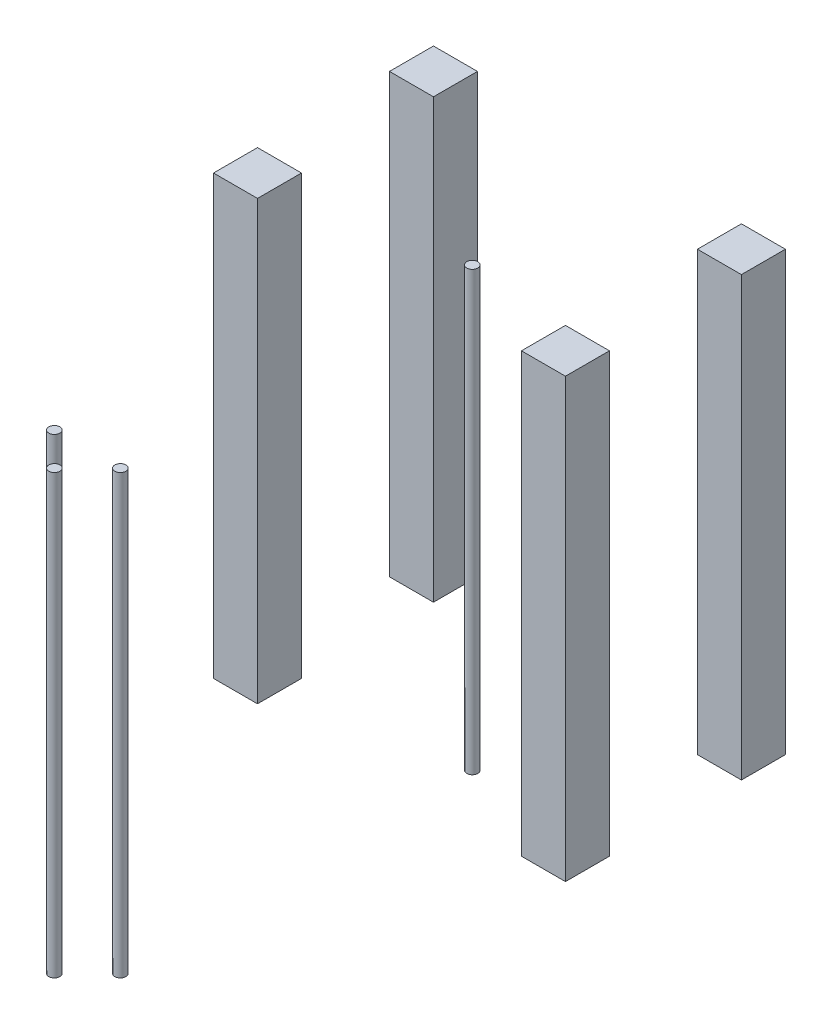
SolidWorks part; units mm, degrees
ref_plane "Ebene vorne" through (0, 0, 0) normal (0, 0, 1) x (1, 0, 0)
ref_plane "Ebene oben" through (0, 0, 0) normal (0, 1, 0) x (1, 0, 0)
ref_plane "Ebene rechts" through (0, 0, 0) normal (1, 0, 0) x (0, 0, -1)
sketch "Top" plane through (0, 0, 0) normal (0, 1, 0) x (1, 0, 0)
  line L0 (0, -95) -> (0, -285) construction
  line L1 (55, -285) -> (55, -95)
  line L2 (55, -285) -> (-55, -285)
  line L3 (-55, -285) -> (-55, -95)
  line L4 (55, -95) -> (-55, -95)
  line L5 (55, -285) -> (-55, -95) construction
  line L6 (-55, -285) -> (55, -95) construction
  line L16 (0, -190) -> (0, -150.9424) construction
  line L27 (-30, -285) -> (-30, -255)
  line L28 (-30, -285) -> (30, -285)
  line L29 (30, -285) -> (30, -255)
  line L30 (-30, -255) -> (30, -255)
  line L31 (0, -255) -> (-30, -255)
  line L32 (30, -255) -> (-30, -255)
  line L34 (30, -285) -> (-30, -285)
  line L35 (0, -190) -> (89.9295, -190) construction
  line L36 (30, -95) -> (-30, -95)
  line L39 (0, -125) -> (-30, -125)
  line L40 (-30, -125) -> (30, -125)
  line L41 (30, -95) -> (30, -125)
  line L42 (-30, -95) -> (30, -95)
  line L43 (-30, -95) -> (-30, -125)
  circle A0 centre (-15, -270) radius 3
  circle A1 centre (15, -270) radius 3
  circle A4 centre (15, -270) radius 3
  circle A5 centre (-15, -270) radius 3
  circle A6 centre (-15, -110) radius 3
  circle A7 centre (15, -110) radius 3
  circle A8 centre (15, -110) radius 3
  circle A9 centre (-15, -110) radius 3
  point P33 (0, -190)
sketch "BaseplateHeight" plane through (0, 0, 0) normal (1, 0, 0) x (0, 0, -1)
  line L1 (-95, 205) -> (-285, 205)
  line L2 (-95, 205) -> (-95, 199)
  line L3 (-95, 199) -> (-285, 199)
  line L4 (-285, 205) -> (-285, 199)
  point P4 (-190, 199)
sketch "Skizze3" plane through (0, 0, 0) normal (0, 1, 0) x (1, 0, 0)
  line L1 (-80, -32.65) -> (-60, -32.65)
  line L2 (-80, -32.65) -> (-80, -52.65)
  line L3 (-80, -52.65) -> (-60, -52.65)
  line L4 (-60, -32.65) -> (-60, -52.65)
  line L5 (60, -32.65) -> (80, -32.65)
  line L6 (60, -32.65) -> (60, -52.65)
  line L7 (60, -52.65) -> (80, -52.65)
  line L8 (80, -32.65) -> (80, -52.65)
  line L9 (60, -112.65) -> (80, -112.65)
  line L10 (60, -112.65) -> (60, -132.65)
  line L11 (60, -132.65) -> (80, -132.65)
  line L12 (80, -112.65) -> (80, -132.65)
  line L13 (-80, -112.65) -> (-60, -112.65)
  line L14 (-80, -112.65) -> (-80, -132.65)
  line L15 (-80, -132.65) -> (-60, -132.65)
  line L16 (-60, -112.65) -> (-60, -132.65)
  circle A0 centre (15, -110) radius 2.5
  circle A1 centre (-15, -270) radius 2.5
  circle A2 centre (0, -285) radius 2.5
  circle A3 centre (15, -270) radius 2.5
extrude "Aufsatz-Linear austragen1" add sketch "Skizze3" along normal up to vertex (199 mm away) up to point (0, 199, 285)
